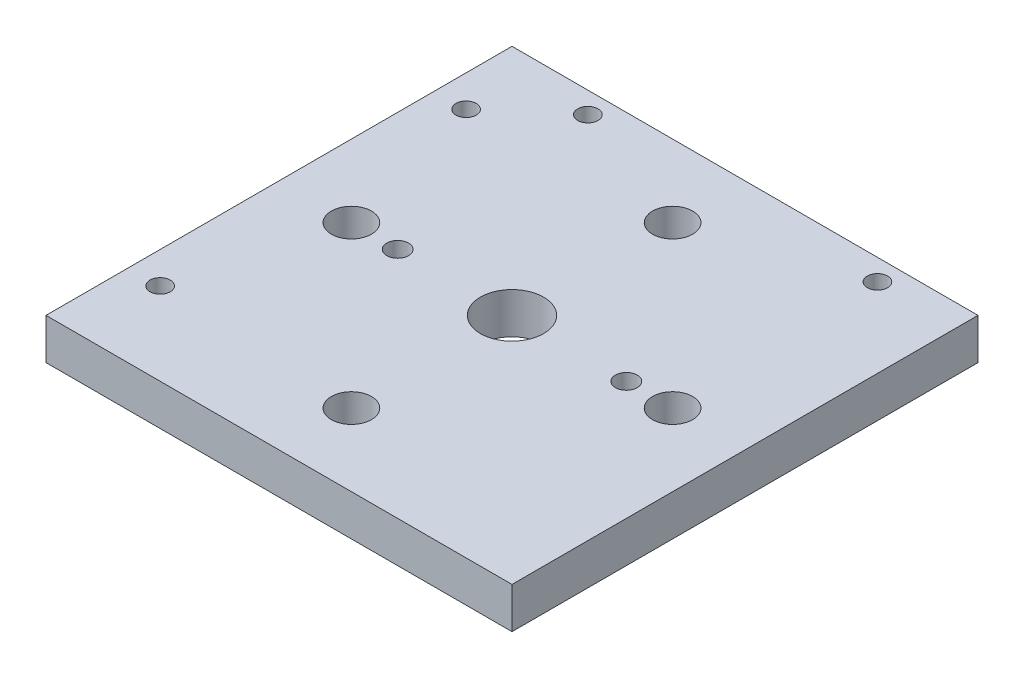
SolidWorks part; units mm, degrees
material "6061 Alloy"
ref_plane "Front Plane" through (0, 0, 0) normal (0, 0, 1) x (1, 0, 0)
ref_plane "Top Plane" through (0, 0, 0) normal (0, 1, 0) x (1, 0, 0)
ref_plane "Right Plane" through (0, 0, 0) normal (1, 0, 0) x (0, 0, -1)
sketch "Sketch1" plane through (0, 0, 0) normal (0, 1, 0) x (1, 0, 0)
  line L5 (-36.85, 36.85) -> (36.85, 36.85)
  line L6 (-36.85, 36.85) -> (-36.85, -36.85)
  line L7 (-36.85, -36.85) -> (36.85, -36.85)
  line L8 (36.85, 36.85) -> (36.85, -36.85)
  circle A0 centre (0, 25.4) radius 3.175
  circle A2 centre (25.4, 0) radius 3.175
  circle A3 centre (0, -25.4) radius 3.175
  circle A4 centre (-25.4, 0) radius 3.175
  circle A5 centre (0, 0) radius 5
  circle A6 centre (24.3099, 33.4852) radius 1.6048
  circle A7 centre (-21.488, 33.4852) radius 1.6048
  circle A8 centre (-31.8573, 24.5972) radius 1.6048
  circle A9 centre (-31.8573, -23.793) radius 1.6048
  point P0 (0, 0)
  point P5 (-18.08, 0)
  point P9 (18.08, 0)
  point P17 (0, 0)
  point P27 (0, 0)
  point P28 (0, 0)
  dimension "D3" = 6.35
  dimension "D7" = 10
  dimension "D1" = 73.7
  dimension "D2" = 73.7
  dimension "D4" = 25.4
  dimension "D6" = 25.4
  dimension "D8" = 36.85
  dimension "D9" = 36.85
  dimension "D10" = 18.77
  dimension "D11" = 18.77
  dimension "D5" = 4
extrude "optical_mount" add sketch "Sketch1" along normal blind 6.477
hole_wizard "#8-32 Tapped Hole1" positions "3DSketch1" profile "Sketch2" tap size "#8-32" standard "ANSI Inch" end condition through all
sketch3d "3DSketch1"
  point P0 (-18.08, 6.477, 0)
  point P2 (18.08, 6.477, 0)
sketch "Sketch2" plane through (-18.08, 6.477, 0) normal (1, 0, 0) x (0, 0, 1)
  line L0 (0, 0) -> (0, 6.477)
  line L1 (0, 6.477) -> (1.7272, 6.477)
  line L2 (1.7272, 6.477) -> (1.7272, 0)
  line L5 (1.7272, 0) -> (0, 0)
  line L11 (0, -6.35) -> (0, 107.95) construction
  dimension "Thru Tap Drill Dia." = 3.4544
  dimension "Thru Tap Drill Depth" = 6.477
cosmetic thread "Hole Thread1" parameters "D2"=4.1656
cosmetic thread "Hole Thread2" parameters "D2"=4.1656
equation "\"D2@Sketch1\"=\"D1@Sketch1\""
equation "\"D8@Sketch1\"=\"D1@Sketch1\"/2"
equation "\"D9@Sketch1\"=\"D8@Sketch1\""
equation "\"D11@Sketch1\"=\"D10@Sketch1\""
